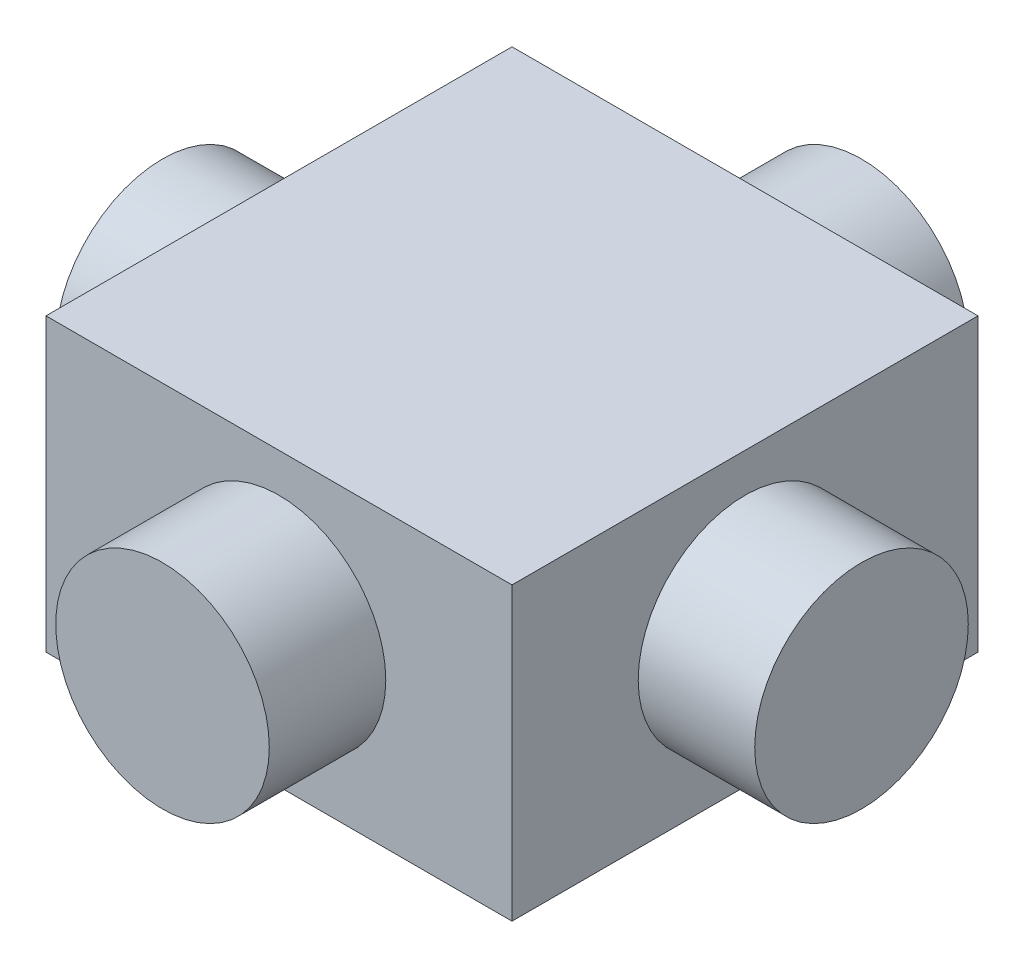
SolidWorks part; units mm, degrees
ref_plane "Front Plane" through (0, 0, 0) normal (0, 0, 1) x (1, 0, 0)
ref_plane "Top Plane" through (0, 0, 0) normal (0, 1, 0) x (1, 0, 0)
ref_plane "Right Plane" through (0, 0, 0) normal (1, 0, 0) x (0, 0, -1)
sketch "Sketch1" plane through (0, 0, 0) normal (0, 0, 1) x (1, 0, 0)
  circle A0 centre (0, 0) radius 1.1
  dimension "D1" = 2.2
extrude "Boss-Extrude1" add sketch "Sketch1" along normal mid plane 7.2
ref_axis "Axis1" through (0, -1.485, 0) along (0, 1, 0)
pattern_circular "CirPattern1" count 4 over 360 about axis through (0, -1.485, 0) along (0, 1, 0) of "Boss-Extrude1"
sketch "Sketch3" plane through (0, 0, 0) normal (0, 1, 0) x (1, 0, 0)
  line L0 (-2.4, -2.4) -> (-2.4, 2.4)
  line L1 (1.1, -1.1) -> (-1.1, -1.1)
  line L2 (1.1, -1.1) -> (1.1, 1.1)
  line L3 (1.1, 1.1) -> (-1.1, 1.1)
  line L4 (-1.1, -1.1) -> (-1.1, 1.1)
  line L5 (1.1, -1.1) -> (-1.1, 1.1) construction
  line L6 (1.1, 1.1) -> (-1.1, -1.1) construction
  line L7 (2.4, 2.4) -> (-2.4, 2.4)
  line L8 (2.4, -2.4) -> (2.4, 2.4)
  line L9 (2.4, -2.4) -> (-2.4, -2.4)
  point P0 (0, 0)
  point P7 (-1.35, 1.35)
  dimension "D2" = 2.2
  dimension "D1" = 1.3
extrude "Boss-Extrude2" add sketch "Sketch3" along normal mid plane 3 contours L4 L1 L2 L3 | L9 L8 L7 L0 L1 L4 L3 L2
